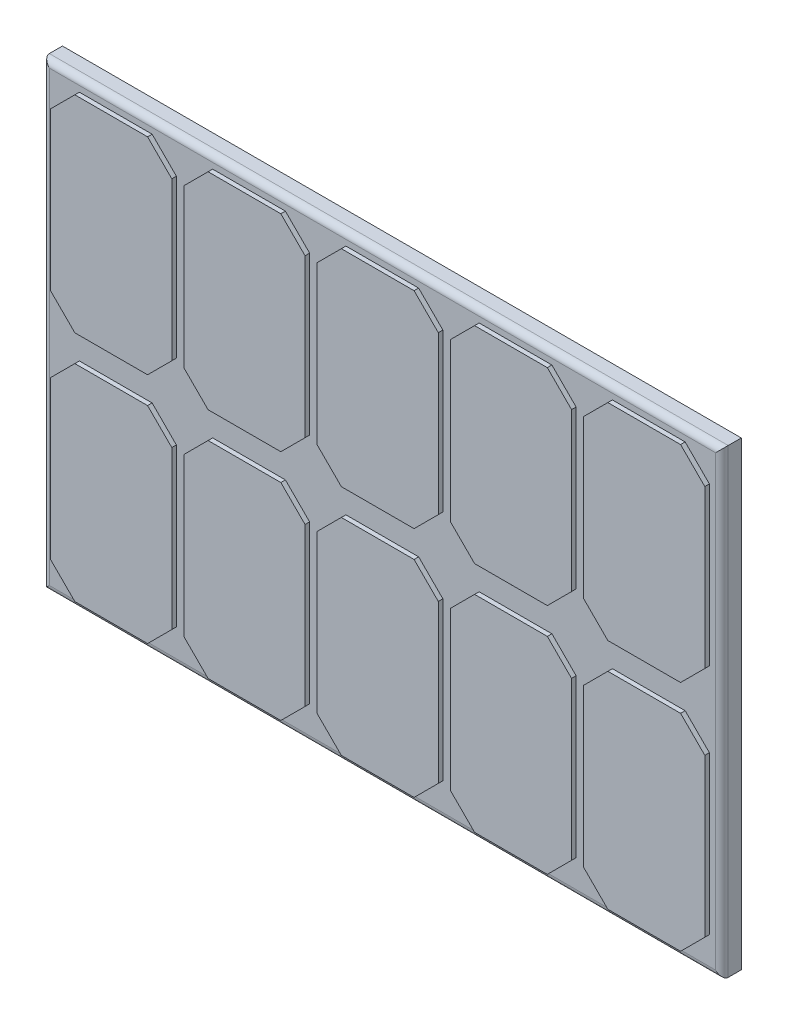
SolidWorks part; units mm, degrees
ref_plane "Front Plane" through (0, 0, 0) normal (0, 0, 1) x (1, 0, 0)
ref_plane "Top Plane" through (0, 0, 0) normal (0, 1, 0) x (1, 0, 0)
ref_plane "Right Plane" through (0, 0, 0) normal (1, 0, 0) x (0, 0, -1)
sketch "Sketch1" plane through (0, 0, 0) normal (0, 0, 1) x (1, 0, 0)
  line L1 (44.45, -30.1625) -> (-44.45, -30.1625)
  line L2 (44.45, -30.1625) -> (44.45, 30.1625)
  line L3 (44.45, 30.1625) -> (-44.45, 30.1625)
  line L4 (-44.45, -30.1625) -> (-44.45, 30.1625)
  line L5 (44.45, -30.1625) -> (-44.45, 30.1625) construction
  line L6 (44.45, 30.1625) -> (-44.45, -30.1625) construction
  point P0 (0, 0)
  dimension "D1" = 60.325
  dimension "D2" = 88.9
extrude "SolarPanelPlasticBase" add sketch "Sketch1" along normal blind 2.54
sketch "Sketch2" plane through (0, 0, 2.54) normal (0, 0, 1) x (1, 0, 0)
  line L3 (44.45, 30.1625) -> (-44.45, 30.1625) construction
  line L8 (-44.45, 30.1625) -> (-44.45, -30.1625) construction
  line L10 (-44.45, 0) -> (-25.4, 30.1625) construction
  line L11 (-39.6875, 28.575) -> (-30.1625, 28.575)
  line L12 (-42.8625, 25.4) -> (-42.8625, 4.7625)
  line L13 (-39.6875, 1.5875) -> (-30.1625, 1.5875)
  line L14 (-26.9875, 25.4) -> (-26.9875, 4.7625)
  line L15 (-42.8625, 28.575) -> (-26.9875, 1.5875) construction
  line L16 (-42.8625, 1.5875) -> (-26.9875, 28.575) construction
  line L17 (-39.6875, 28.575) -> (-42.8625, 25.4)
  line L18 (-30.1625, 28.575) -> (-26.9875, 25.4)
  line L19 (-26.9875, 4.7625) -> (-30.1625, 1.5875)
  line L20 (-42.8625, 4.7625) -> (-39.6875, 1.5875)
  point P24 (-34.925, 15.0812)
  point P29 (-34.925, 15.0812)
  dimension "D4" = 1.5875
extrude "CrystalElement" add sketch "Sketch2" along normal blind 0.5969
fillet "OutsideFillet" radius 0.8255 4 edges at (0, -30.1625, 2.54) (44.45, 0, 2.54) (-44.45, 0, 2.54) (0, 30.1625, 2.54)
pattern_linear "LPattern1" count 5 spacing 17.4498 along (1, 0, 0) count 2 spacing 30.48 along (0, -1, 0) of "CrystalElement"
